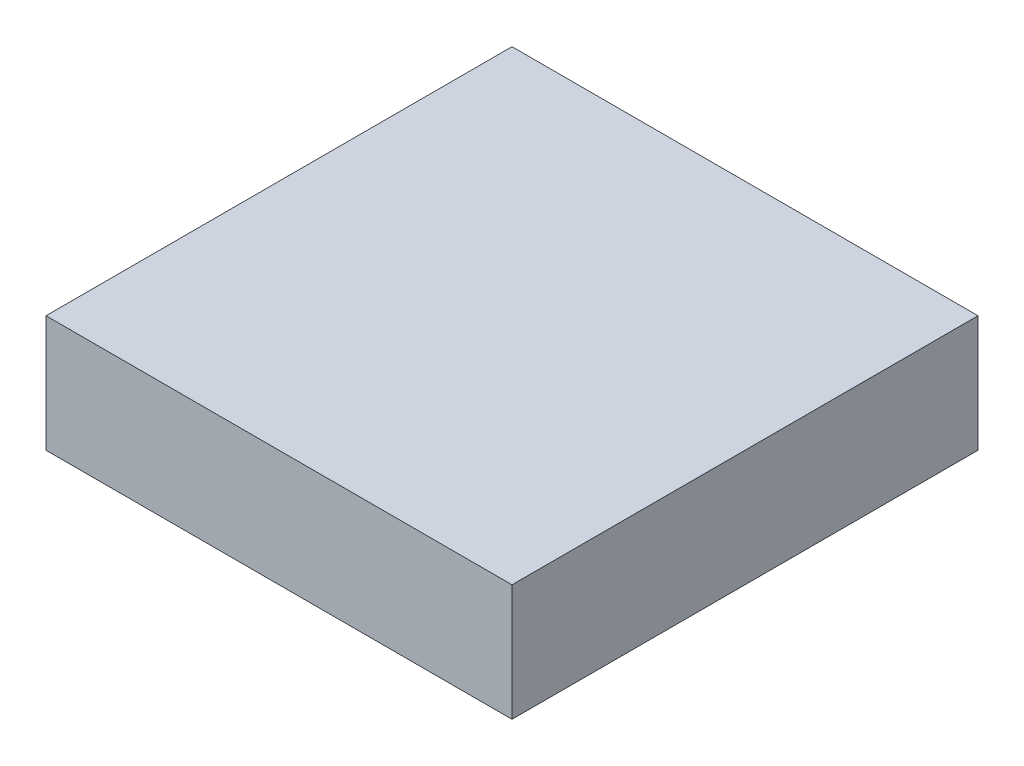
SolidWorks part; units mm, degrees
ref_plane "Front Plane" through (0, 0, 0) normal (0, 0, 1) x (1, 0, 0)
ref_plane "Top Plane" through (0, 0, 0) normal (0, 1, 0) x (1, 0, 0)
ref_plane "Right Plane" through (0, 0, 0) normal (1, 0, 0) x (0, 0, -1)
sketch "Sketch1" plane through (0, 0, 0) normal (0, 1, 0) x (1, 0, 0)
  line L1 (-6096, 6096) -> (6096, 6096)
  line L2 (-6096, 6096) -> (-6096, -6096)
  line L3 (-6096, -6096) -> (6096, -6096)
  line L4 (6096, 6096) -> (6096, -6096)
  dimension "D1" = 6096
  dimension "D2" = 6096
  dimension "D3" = 6096
  dimension "D4" = 6096
extrude "Boss-Extrude1" add sketch "Sketch1" against normal blind 3048
